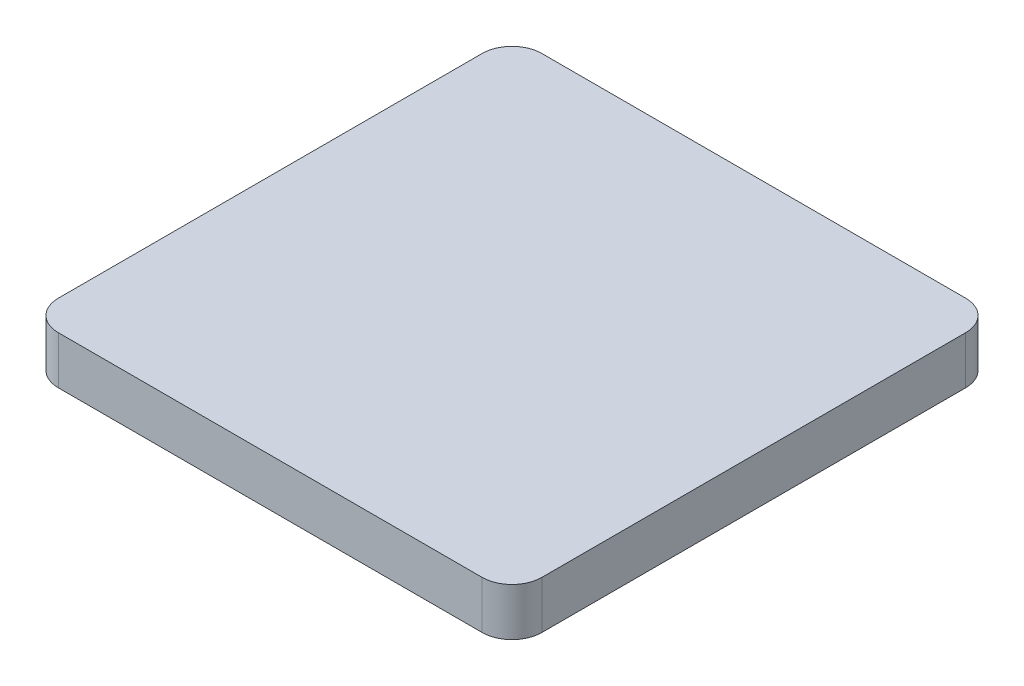
SolidWorks part; units mm, degrees
ref_plane "Front Plane" through (0, 0, 0) normal (0, 0, 1) x (1, 0, 0)
ref_plane "Top Plane" through (0, 0, 0) normal (0, 1, 0) x (1, 0, 0)
ref_plane "Right Plane" through (0, 0, 0) normal (1, 0, 0) x (0, 0, -1)
sketch "Sketch1" plane through (0, 0, 0) normal (0, 1, 0) x (1, 0, 0)
  line L0 (22.5, 36.5) -> (-32.5, 36.5)
  line L1 (-36.5, 32.5) -> (-36.5, -32.5)
  line L2 (-32.5, -36.5) -> (32.5, -36.5)
  line L3 (36.5, -32.5) -> (36.5, 32.5)
  arc A0 (22.5, 36.5) -> (32.5, 36.5) centre (27.5, 36.5) ccw
  arc A1 (-32.5, 36.5) -> (-36.5, 32.5) centre (-32.5, 32.5) ccw
  arc A2 (-36.5, -32.5) -> (-32.5, -36.5) centre (-32.5, -32.5) ccw
  arc A3 (32.5, -36.5) -> (36.5, -32.5) centre (32.5, -32.5) ccw
  arc A4 (36.5, 32.5) -> (32.5, 36.5) centre (32.5, 32.5) ccw
  point P15 (-36.5, 32.5)
  point P16 (-32.5, 36.5)
  point P17 (0, 0)
  point P18 (0, 0)
  point P19 (0, 0)
  point P20 (0, 0)
  point P21 (0, 0)
  point P22 (0, 0)
  point P23 (0, 0)
  point P24 (0, 0)
  point P25 (0, 0)
  point P26 (0, 0)
  point P27 (0, 0)
  dimension "D3" = 4
  dimension "D4" = 5
  dimension "D9" = 4
  dimension "D1" = 36.5
  dimension "D2" = 36.5
  dimension "D5" = 9
  dimension "D6" = 73
  dimension "D7" = 73
  dimension "D8" = 10
sketch "Sketch2" plane through (0, 0, 0) normal (0, 1, 0) x (1, 0, 0)
  line L0 (22.5, 36.5) -> (-32.5, 36.5) construction
  line L1 (-40.5, -40.5) -> (40.5, -40.5)
  line L2 (-40.5, -40.5) -> (-40.5, 40.5)
  line L3 (-40.5, 40.5) -> (40.5, 40.5)
  line L4 (40.5, -40.5) -> (40.5, 40.5)
  line L5 (-40.5, -40.5) -> (40.5, 40.5) construction
  line L6 (-40.5, 40.5) -> (40.5, -40.5) construction
  line L7 (-36.5, 32.5) -> (-36.5, -32.5) construction
  point P0 (0, 0)
  dimension "D1" = 4
  dimension "D2" = 4
extrude "Boss-Extrude1" add sketch "Sketch2" along normal mid plane 8 contours L1 L4 L3 L2
extrude "Cut-Extrude1" cut sketch "Sketch1" against normal blind 4
fillet "Fillet1" radius 5 4 edges at (40.5, 0, 40.5) (40.5, 0, -40.5) (-40.5, 0, -40.5) (-40.5, 0, 40.5)
